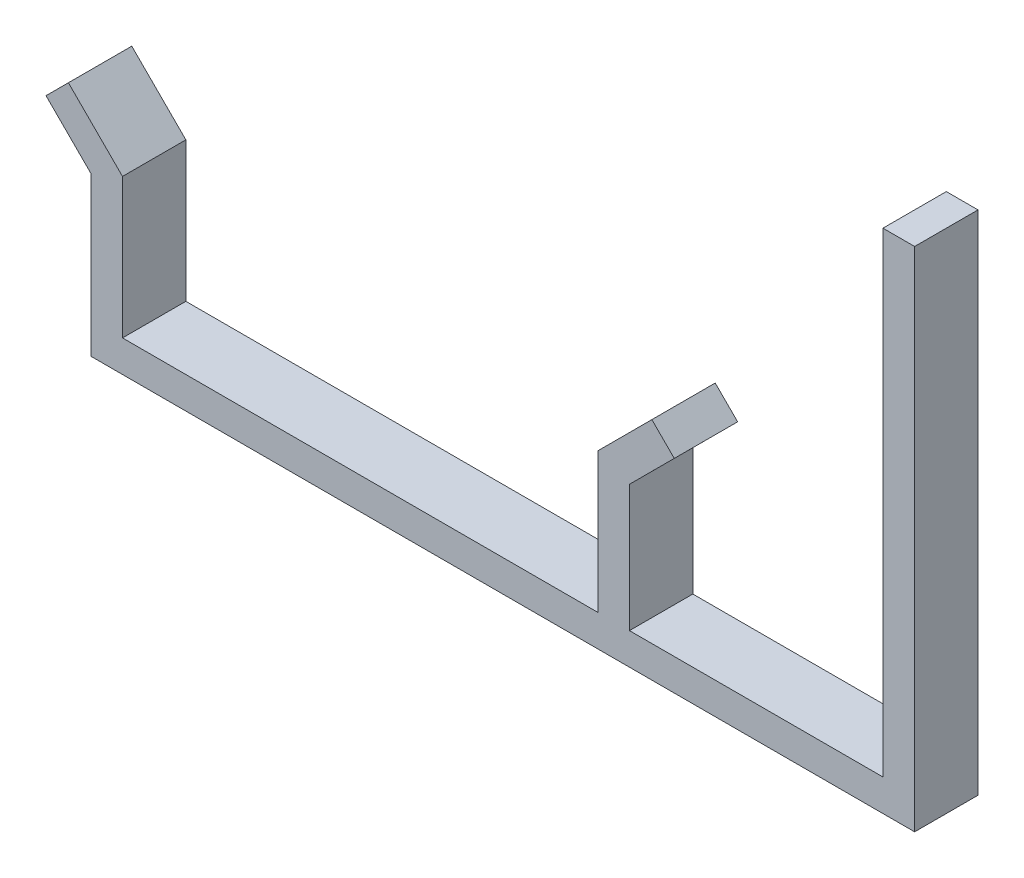
SolidWorks part; units mm, degrees
ref_plane "Front Plane" through (0, 0, 0) normal (0, 0, 1) x (1, 0, 0)
ref_plane "Top Plane" through (0, 0, 0) normal (0, 1, 0) x (1, 0, 0)
ref_plane "Right Plane" through (0, 0, 0) normal (1, 0, 0) x (0, 0, -1)
sketch "Sketch6" plane through (0, 0, 0) normal (0, 0, 1) x (1, 0, 0)
  line L0 (-61.4643, -8.0581) -> (-61.4643, -33.0581)
  line L1 (-61.4643, -33.0581) -> (68.5359, -33.0581)
  line L2 (68.5359, -33.0581) -> (68.5359, 46.9419)
  line L3 (63.5359, -28.0581) -> (63.5359, 46.9419)
  line L4 (63.5359, 46.9419) -> (68.5359, 46.9419)
  line L5 (63.5359, -28.0581) -> (23.5359, -28.0581)
  line L6 (-61.4643, -8.0581) -> (-68.5359, -0.9876)
  line L7 (23.5359, -28.0581) -> (23.5359, -8.0581)
  line L8 (23.5359, -8.0581) -> (30.6064, -0.9865)
  line L9 (30.6064, -0.9865) -> (27.0706, 2.5488)
  line L10 (18.5357, -28.0581) -> (18.5357, -5.9875)
  line L11 (18.5357, -5.9875) -> (27.0706, 2.5488)
  line L12 (18.5357, -28.0581) -> (-56.4643, -28.0581)
  line L13 (-56.4643, -28.0581) -> (-56.4643, -5.987)
  line L14 (-56.4643, -5.987) -> (-65.001, 2.5485)
  line L15 (-68.5359, -0.9876) -> (-65.001, 2.5485)
  line L16 (-37.2643, 15.8182) -> (-37.2643, -46.9419) construction
extrude "Boss-Extrude4" add sketch "Sketch6" along normal blind 10
sketch "Sketch7" plane through (68.5359, 0, 0) normal (1, 0, 0) x (0, 0, -1)
  circle A0 centre (-5, 6.9419) radius 3
